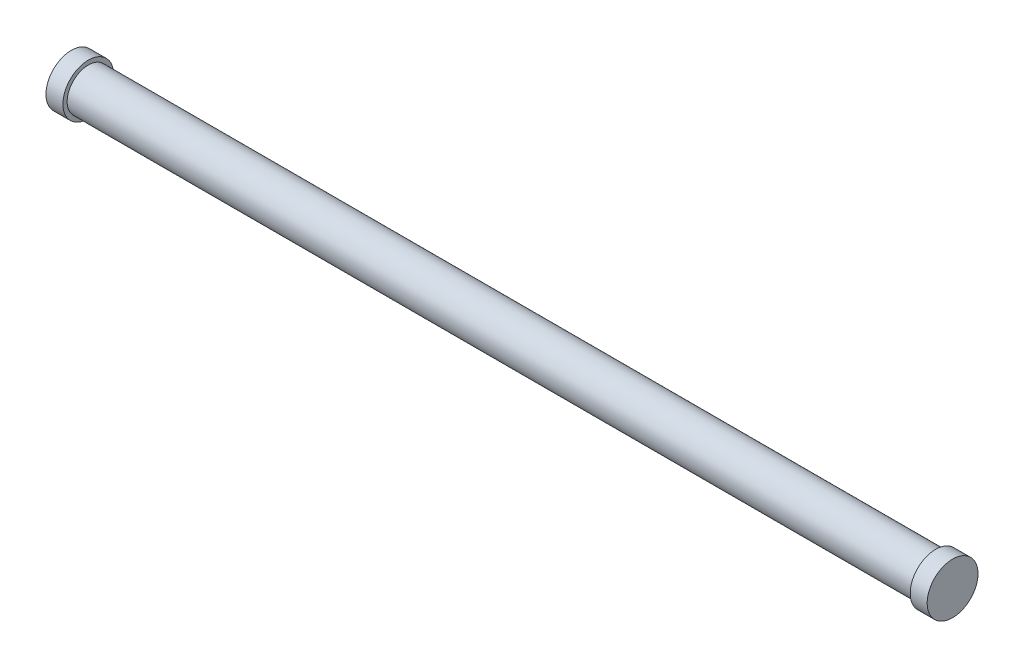
SolidWorks part; units mm, degrees
material "3003 Alloy"
ref_plane "Front Plane" through (0, 0, 0) normal (0, 0, 1) x (1, 0, 0)
ref_plane "Top Plane" through (0, 0, 0) normal (0, 1, 0) x (1, 0, 0)
ref_plane "Right Plane" through (0, 0, 0) normal (1, 0, 0) x (0, 0, -1)
sketch "Sketch1" plane through (0, 0, 0) normal (1, 0, 0) x (0, 0, -1)
  circle A0 centre (0, 0) radius 0.762
extrude "Boss-Extrude1" add sketch "Sketch1" along normal blind 0.508
sketch "Sketch2" plane through (0.508, 0, 0) normal (1, 0, 0) x (0, 0, -1)
  circle A0 centre (0, 0) radius 0.635
extrude "Boss-Extrude2" add sketch "Sketch2" along normal blind 25.4
sketch "Sketch3" plane through (25.908, 0, 0) normal (1, 0, 0) x (0, 0, -1)
  circle A0 centre (0, 0) radius 0.762
extrude "Boss-Extrude3" add sketch "Sketch3" along normal blind 0.508
